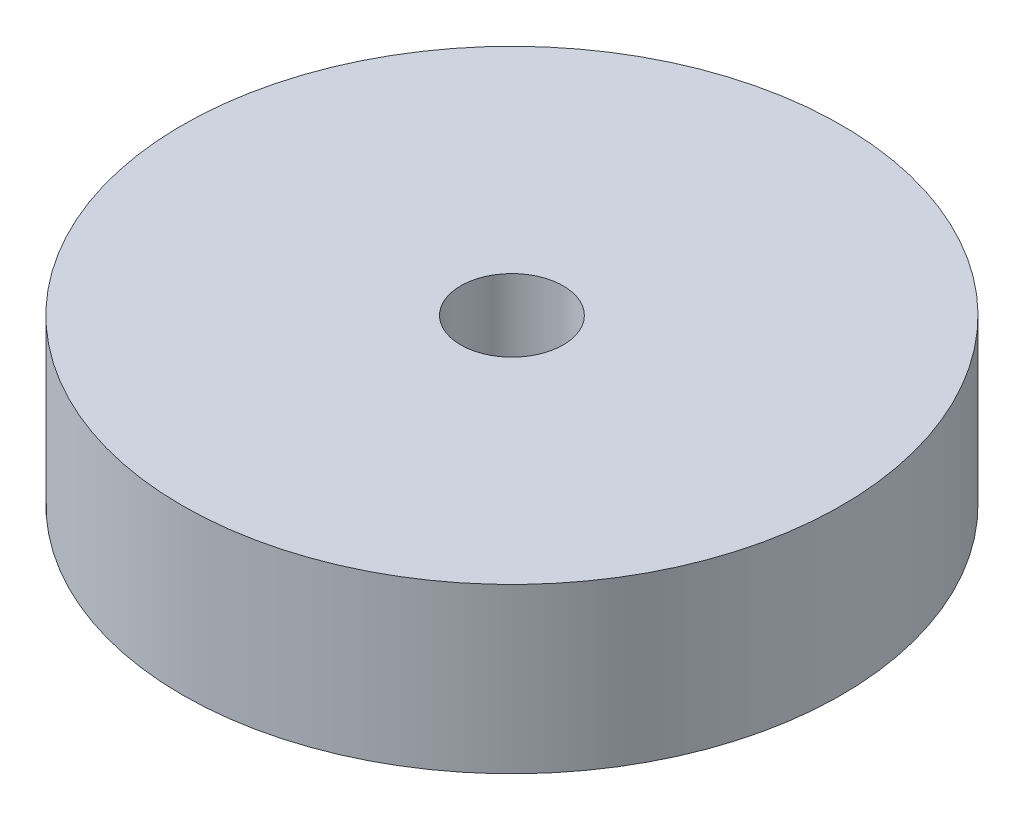
SolidWorks part; units mm, degrees
ref_plane "Front Plane" through (0, 0, 0) normal (0, 0, 1) x (1, 0, 0)
ref_plane "Top Plane" through (0, 0, 0) normal (0, 1, 0) x (1, 0, 0)
ref_plane "Right Plane" through (0, 0, 0) normal (1, 0, 0) x (0, 0, -1)
sketch "Sketch1" plane through (0, 0, 0) normal (0, 0, 1) x (1, 0, 0)
  line L0 (0, 0) -> (0, -10.7101) construction
  line L1 (-1.5875, 0) -> (-10.2108, 0)
  line L2 (-1.5875, 0) -> (-1.5875, -5.08)
  line L3 (-1.5875, -5.08) -> (-10.2108, -5.08)
  line L4 (-10.2108, 0) -> (-10.2108, -5.08)
  dimension "D1" = 1.5875
  dimension "D2" = 10.2108
  dimension "D3" = 5.08
revolve "Revolve1" add sketch "Sketch1" angle 360 about L0
